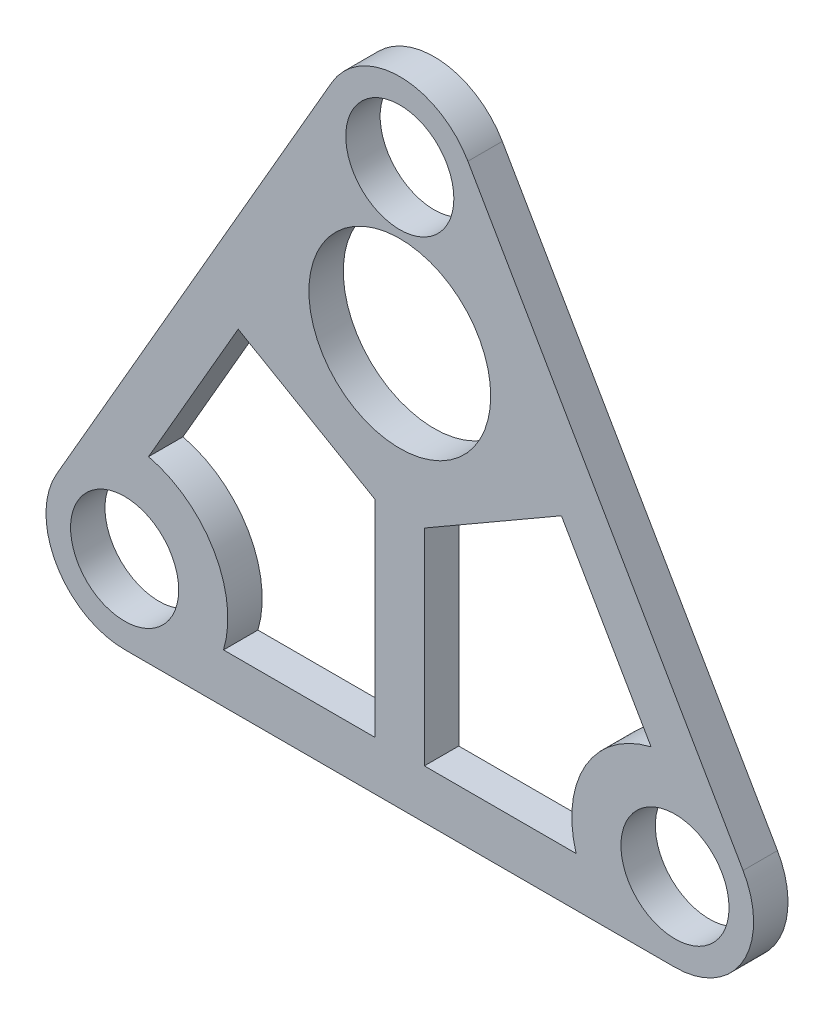
SolidWorks part; units mm, degrees
ref_plane "Front Plane" through (0, 0, 0) normal (0, 0, 1) x (1, 0, 0)
ref_plane "Top Plane" through (0, 0, 0) normal (0, 1, 0) x (1, 0, 0)
ref_plane "Right Plane" through (0, 0, 0) normal (1, 0, 0) x (0, 0, -1)
sketch "Sketch1" plane through (0, 0, 0) normal (0, 0, 1) x (1, 0, 0)
  line L0 (3.85, 0) -> (-3.85, 0) construction
  line L1 (42.1436, 104.9948) -> (-13.8564, 8)
  line L2 (69.8564, 104.9948) -> (125.8564, 8)
  line L3 (0, -16) -> (112, -16)
  circle A0 centre (0, 0) radius 11
  circle A1 centre (112, 0) radius 11
  arc A2 (-13.8564, 8) -> (0, -16) centre (0, 0) ccw
  arc A3 (112, -16) -> (125.8564, 8) centre (112, 0) ccw
  circle A4 centre (56, 96.9948) radius 11
  arc A5 (69.8564, 104.9948) -> (42.1436, 104.9948) centre (56, 96.9948) ccw
  dimension "D1" = 22
  dimension "D2" = 22
  dimension "D3" = 32
  dimension "D4" = 32
  dimension "D5" = 112
  dimension "D6" = 22
  dimension "D7" = 32
  dimension "D8" = 112
  dimension "D9" = 112
extrude "Boss-Extrude1" add sketch "Sketch1" along normal blind 7
sketch "Sketch3" plane through (0, 0, 7) normal (0, 0, 1) x (1, 0, 0)
  line L0 (56, 71.0948) -> (56, 69.0948) construction
  circle A0 centre (56, 96.9948) radius 27.9 construction
  circle A1 centre (56, 65.9448) radius 5.15 construction
  circle A2 centre (56, 65.9448) radius 18.5
  dimension "D1" = 55.8
  dimension "D2" = 10.3
  dimension "D4" = 37
  dimension "D3" = 2
extrude "Cut-Extrude1" cut sketch "Sketch3" against normal through all
sketch "Sketch6" plane through (0, 0, 0) normal (0, 0, 1) x (1, 0, 0)
  line L0 (23.1088, 52.0256) -> (4.8662, 20.4284)
  line L2 (20.1246, -6) -> (51, -6)
  line L3 (23.1088, 52.0256) -> (51, 35.9226)
  line L4 (51, 35.9226) -> (51, -6)
  line L5 (61, 35.9226) -> (61, -6)
  line L9 (88.8912, 52.0256) -> (107.1338, 20.4284)
  line L11 (88.8912, 52.0256) -> (61, 35.9226)
  line L13 (61, -6) -> (91.8754, -6)
  line L14 (0, -16) -> (112, -16) construction
  line L15 (42.1436, 104.9948) -> (-13.8564, 8) construction
  line L16 (125.8564, 8) -> (69.8564, 104.9948) construction
  line L17 (35.0907, 56.6549) -> (56, 44.5829) construction
  line L18 (76.6153, 56.4851) -> (56, 44.5829) construction
  arc A0 (20.1246, -6) -> (4.8662, 20.4284) centre (0, 0) ccw
  arc A2 (107.1338, 20.4284) -> (91.8754, -6) centre (112, 0) ccw
  circle A4 centre (112, 0) radius 11 construction
  circle A5 centre (0, 0) radius 11 construction
  circle A7 centre (56, 65.9448) radius 18.5 construction
  dimension "D1" = 10
  dimension "D5" = 10
  dimension "D2" = 10
  dimension "D6" = 10
  dimension "D3" = 10
  dimension "D4" = 10
  dimension "D7" = 10
  dimension "D8" = 10
extrude "Cut-Extrude3" cut sketch "Sketch6" along normal through all
